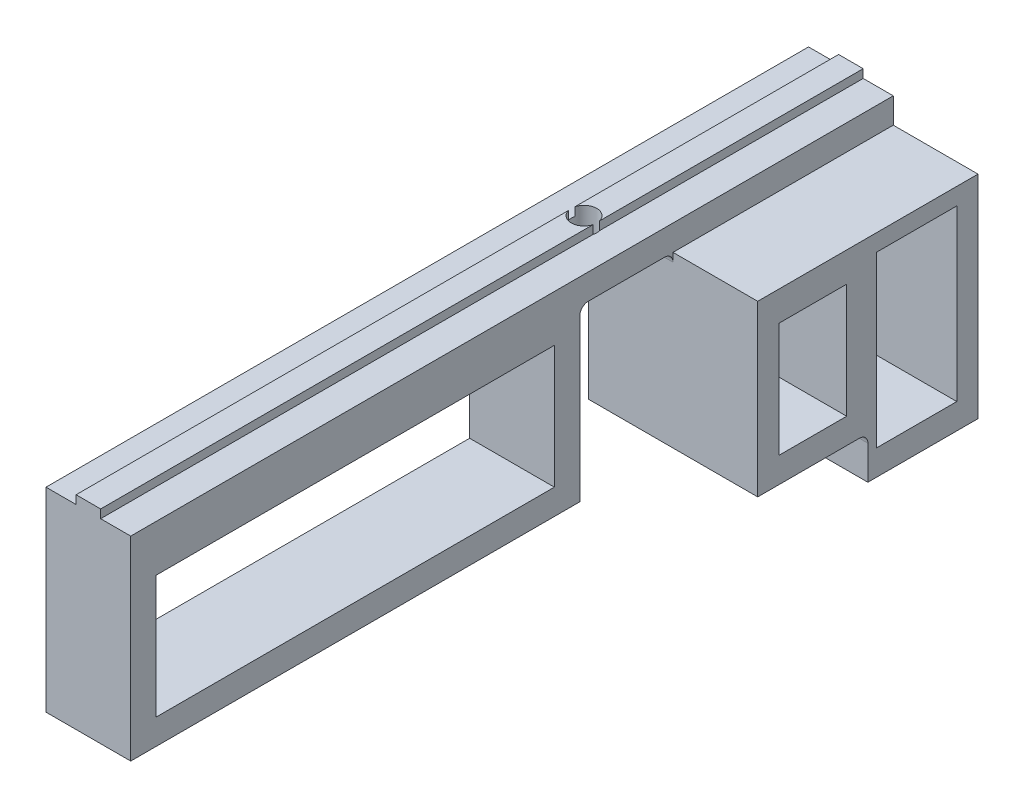
SolidWorks part; units mm, degrees
ref_plane "Front Plane" through (0, 0, 0) normal (0, 0, 1) x (1, 0, 0)
ref_plane "Top Plane" through (0, 0, 0) normal (0, 1, 0) x (1, 0, 0)
ref_plane "Right Plane" through (0, 0, 0) normal (1, 0, 0) x (0, 0, -1)
sketch "Sketch1" plane through (0, 0, 0) normal (0, 0, 1) x (1, 0, 0)
  line L0 (-5, 0) -> (5, 0)
  line L1 (5, 0) -> (5, 3)
  line L2 (5, 3) -> (1.45, 3)
  line L3 (1.45, 3) -> (1.45, 4)
  line L4 (1.45, 4) -> (-1.45, 4)
  line L5 (-1.45, 4) -> (-1.45, 3)
  line L6 (-1.45, 3) -> (-5, 3)
  line L7 (-5, 3) -> (-5, 0)
  point P9 (0, 0)
  dimension "D1" = 10
  dimension "D2" = 2.9
  dimension "D3" = 3
  dimension "D4" = 1
extrude "MakerBeamFix" add sketch "Sketch1" along normal mid plane 90
sketch "Sketch2" plane through (0, 0, 0) normal (0, -1, 0) x (-1, 0, 0)
  line L0 (-5, -45) -> (-1.45, -45) construction
  circle A0 centre (0, 13.5) radius 1.5
  point P2 (0, -12.4563)
  point P3 (0, 11.0544)
  point P8 (-3.225, -45)
  dimension "D1" = 3
  dimension "D2" = 58.5
extrude "MakerBeamFixHole" cut sketch "Sketch2" against normal through all
sketch "Sketch3" plane through (-5, 0, 0) normal (-1, 0, 0) x (0, 0, 1)
  line L1 (-32, -25) -> (-45, -25)
  line L2 (-32, -25) -> (-32, 0)
  line L3 (-32, 0) -> (-45, 0)
  line L4 (-45, -25) -> (-45, 0)
  line L5 (-32, -25) -> (-45, 0) construction
  line L6 (-32, 0) -> (-45, -25) construction
  line L7 (-42.5, -2) -> (-33, -2)
  line L8 (-42.5, -2) -> (-42.5, -22)
  line L9 (-42.5, -22) -> (-33, -22)
  line L10 (-33, -2) -> (-33, -22)
  point P0 (-38.5, -12.5)
  dimension "D1" = 9.5
  dimension "D2" = 13
  dimension "D3" = 25
  dimension "D4" = 20
  dimension "D5" = 3
  dimension "D6" = 2.5
extrude "MakerBeamToolPlatePlier" add sketch "Sketch3" against normal blind 20
sketch "Sketch4" plane through (-5, 0, 0) normal (-1, 0, 0) x (0, 0, 1)
  line L0 (45, 0) -> (-32, 0) construction
  line L1 (-32, 0) -> (-19, 0)
  line L2 (-32, 0) -> (-32, -20)
  line L3 (-32, -20) -> (-19, -20)
  line L4 (-19, 0) -> (-19, -20)
  line L5 (-32, 0) -> (-19, -20) construction
  line L6 (-32, -20) -> (-19, 0) construction
  line L8 (45, 0) -> (-32, 0) construction
  line L9 (-29.5, -3.5) -> (-21.5, -3.5)
  line L10 (-29.5, -3.5) -> (-29.5, -17)
  line L11 (-29.5, -17) -> (-21.5, -17)
  line L12 (-21.5, -3.5) -> (-21.5, -17)
  line L13 (-32, -25) -> (-32, 0) construction
  point P0 (-25.5, -10)
  point P10 (-22.0609, 0)
  point P11 (-20, 0)
  point P15 (-15.9699, -20)
  point P16 (-20, 0)
  dimension "D1" = 20
  dimension "D2" = 13
  dimension "D4" = 13.5
  dimension "D5" = 3
  dimension "D6" = 8
  dimension "D7" = 2.5
extrude "MakerBeamToolCutPlier" add sketch "Sketch4" against normal blind 20
sketch "Sketch5" plane through (-5, 0, 0) normal (-1, 0, 0) x (0, 0, 1)
  line L0 (45, 0) -> (-19, 0) construction
  line L1 (-8, 0) -> (45, 0)
  line L2 (-8, 0) -> (-8, -20)
  line L3 (-8, -20) -> (45, -20)
  line L4 (45, 0) -> (45, -20)
  line L5 (-5, -2.5) -> (42, -2.5)
  line L6 (-5, -2.5) -> (-5, -17)
  line L7 (-5, -17) -> (42, -17)
  line L8 (42, -2.5) -> (42, -17)
  line L9 (45, 3) -> (45, 0) construction
  point P8 (61.8743, -20.0502)
  point P9 (-29.0575, -0.6971)
  point P10 (25, 0)
  dimension "D1" = 53
  dimension "D2" = 47
  dimension "D3" = 14.5
  dimension "D4" = 20
  dimension "D5" = 3
  dimension "D6" = 3
extrude "BigFacomPlier" add sketch "Sketch5" against normal blind 10
fillet "Fillet1" radius 1 3 edges at (0, 0, -8) (0, 0, -19) (5, -20, -32)
